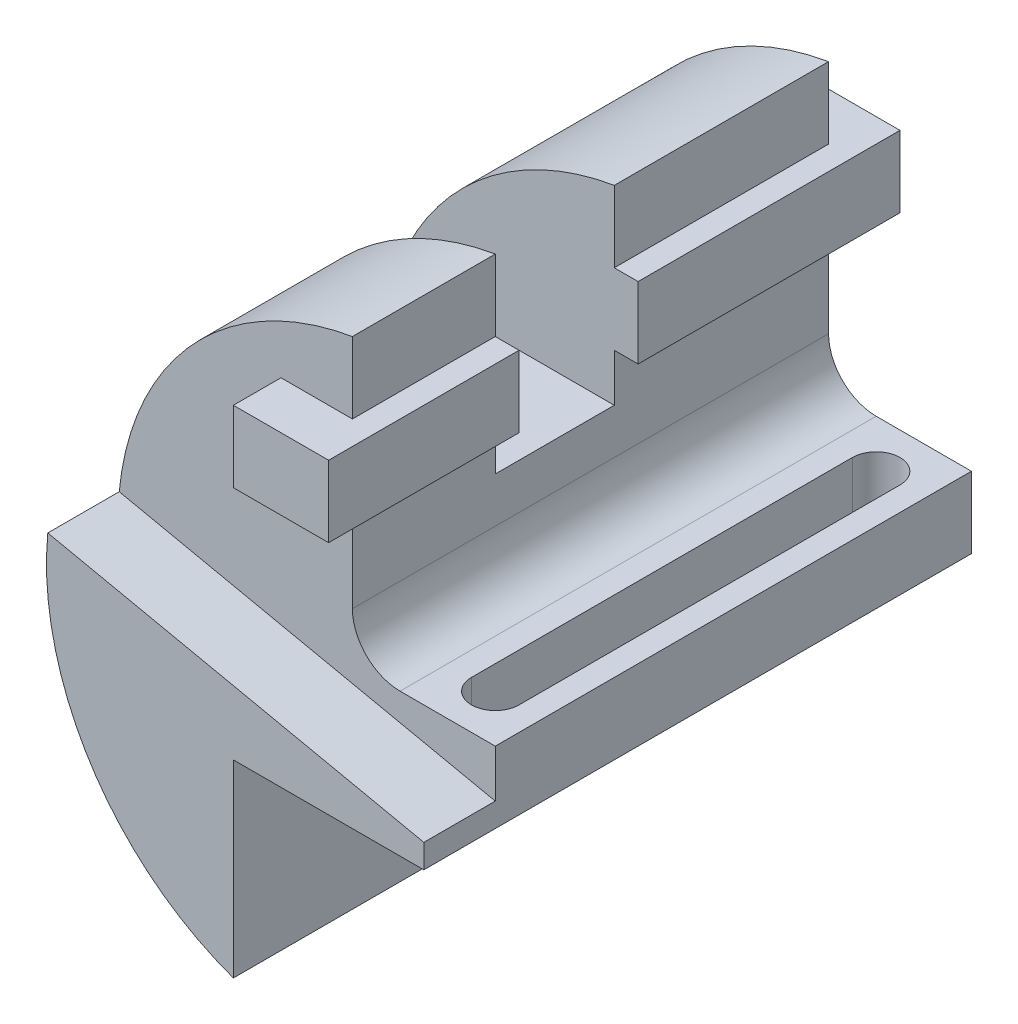
SolidWorks part; units mm, degrees
material "1060 Alloy"
ref_plane "Front Plane" through (0, 0, 0) normal (0, 0, 1) x (1, 0, 0)
ref_plane "Top Plane" through (0, 0, 0) normal (0, 1, 0) x (1, 0, 0)
ref_plane "Right Plane" through (0, 0, 0) normal (1, 0, 0) x (0, 0, -1)
sketch "Sketch1" plane through (0, 0, 0) normal (0, 0, 1) x (1, 0, 0)
  line L0 (-10, 58.4) -> (-10, 43.4)
  line L1 (0, -1.1) -> (20, -1.1)
  line L2 (20, -1.1) -> (20, -16.1)
  line L3 (20, -16.1) -> (-20, -16.1)
  line L4 (-20, -16.1) -> (-20, -55.7724)
  line L5 (-10, 28.4) -> (-10, 8.9)
  line L6 (-25, 43.4) -> (-10, 43.4)
  line L7 (-25, 43.4) -> (-25, 28.4)
  line L8 (-25, 28.4) -> (-10, 28.4)
  arc A0 (-10, 58.4) -> (-20, -55.7724) centre (0, 0) ccw
  arc A1 (-10, 8.9) -> (0, -1.1) centre (0, 8.9) ccw
  dimension "D1" = 10
  dimension "D2" = 59.25
  dimension "D3" = 10
  dimension "D4" = 59.5
  dimension "D5" = 40
  dimension "D6" = 15
  dimension "D7" = 20
  dimension "D8" = 15
  dimension "D9" = 15
  dimension "D10" = 15
extrude "Boss-Extrude1" add sketch "Sketch1" against normal blind 100
sketch "Sketch2" plane through (0, 0, 0) normal (0, 0, 1) x (1, 0, 0)
  line L0 (20, -11.1) -> (-58.9764, 5.687)
  line L1 (20, -16.1) -> (20, -1.1) construction
  line L2 (-20, -16.1) -> (20, -16.1) construction
  line L3 (-20, -55.7724) -> (-20, -16.1) construction
  line L4 (20, -16.1) -> (20, -11.1)
  line L5 (-20, -16.1) -> (20, -16.1)
  line L6 (-20, -55.7724) -> (-20, -16.1)
  arc A0 (-10, 58.4) -> (-20, -55.7724) centre (0, 0) ccw construction
  arc A1 (-58.9764, 5.687) -> (-20, -55.7724) centre (0, 0) ccw
  dimension "D1" = 5
  dimension "D2" = 78
extrude "Boss-Extrude2" add sketch "Sketch2" along normal blind 15
sketch "Sketch3" plane through (0, 0, 0) normal (1, 0, 0) x (0, 0, -1)
  line L0 (0, 43.4) -> (0, 58.4) construction
  line L1 (30, 58.4) -> (55, 58.4)
  line L2 (30, 58.4) -> (30, 18.4)
  line L3 (30, 18.4) -> (55, 18.4)
  line L4 (55, 58.4) -> (55, 18.4)
  line L5 (100, 58.4) -> (0, 58.4) construction
  dimension "D1" = 25
  dimension "D2" = 30
  dimension "D3" = 40
extrude "Cut-Extrude1" cut sketch "Sketch3" against normal through all both and the other way through all
ref_plane "Plane1" through (0, 0, 10) normal (0, 0, 1) x (1, 0, 0)
ref_plane "Plane2" through (0, 0, -110) normal (0, 0, -1) x (-1, 0, 0)
sketch "Sketch4" plane through (0, 0, -55) normal (0, 0, 1) x (1, 0, 0)
  line L0 (-10, 28.4) -> (-25, 28.4) construction
  line L1 (-25, 43.4) -> (-5, 43.4)
  line L2 (-25, 43.4) -> (-25, 28.4)
  line L3 (-25, 28.4) -> (-5, 28.4)
  line L4 (-5, 43.4) -> (-5, 28.4)
  dimension "D1" = 20
  dimension "D2" = 15
extrude "Boss-Extrude3" add sketch "Sketch4" against normal up to surface (55 mm away) up to plane "Plane2"
sketch "Sketch5" plane through (0, 0, -30) normal (0, 0, -1) x (-1, 0, 0)
  line L0 (25, 28.4) -> (25, 43.4) construction
  line L1 (25, 28.4) -> (5, 28.4) construction
  line L2 (5, 28.4) -> (5, 43.4) construction
  line L3 (5, 43.4) -> (25, 43.4) construction
  line L4 (25, 28.4) -> (25, 43.4)
  line L5 (25, 28.4) -> (5, 28.4)
  line L6 (5, 28.4) -> (5, 43.4)
  line L7 (5, 43.4) -> (25, 43.4)
extrude "Boss-Extrude4" add sketch "Sketch5" against normal up to surface (40 mm away) up to plane "Plane1"
sketch "Sketch6" plane through (0, -1.1, 0) normal (0, 1, 0) x (1, 0, 0)
  line L0 (10, 90) -> (10, 10) construction
  line L3 (15, 90) -> (15, 10)
  line L4 (5, 90) -> (5, 10)
  line L5 (20, 0) -> (0, 0) construction
  line L6 (20, 100) -> (0, 100) construction
  line L7 (20, 100) -> (20, 0) construction
  arc A2 (15, 90) -> (5, 90) centre (10, 90) ccw
  arc A3 (5, 10) -> (15, 10) centre (10, 10) ccw
  point P2 (10, 50)
  dimension "D1" = 10
  dimension "D2" = 80
  dimension "D3" = 10
  dimension "D4" = 10
  dimension "D5" = 10
extrude "Cut-Extrude2" cut sketch "Sketch6" along normal through all and the other way through all
equation "\"A\" = 59.25"
equation "\"B\" = 59.5"
equation "\"C\"= 25"
equation "\"D2@Sketch1\"=\"A\""
equation "\"D4@Sketch1\"=\"B\""
equation "\"D1@Sketch3\"=\"C\""
